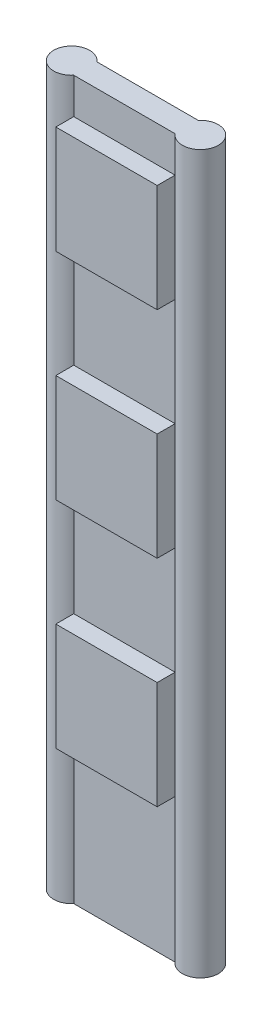
SolidWorks part; units mm, degrees
ref_plane "前基準面" through (0, 0, 0) normal (0, 0, 1) x (1, 0, 0)
ref_plane "上基準面" through (0, 0, 0) normal (0, 1, 0) x (1, 0, 0)
ref_plane "右基準面" through (0, 0, 0) normal (1, 0, 0) x (0, 0, -1)
sketch "草圖2" plane through (0, 0, 0) normal (0, 1, 0) x (1, 0, 0)
  line L0 (0, 120.0549) -> (0, -130.4945) construction
  line L1 (-141.2413, 21.3942) -> (141.2413, 21.3942)
  line L3 (-141.2413, -43.1319) -> (141.2413, -43.1319)
  line L5 (-150, 43.1319) -> (150, -43.1319) construction
  line L6 (-150, -43.1319) -> (150, 43.1319) construction
  arc A0 (-141.2413, 21.3942) -> (-141.2413, -43.1319) centre (-179.4394, -10.8688) ccw
  arc A1 (141.2413, 21.3942) -> (141.2413, -43.1319) centre (179.4394, -10.8688) cw
  point P0 (0, 0)
  point P7 (0, 0)
  dimension "D2" = 50
  dimension "D1" = 300
extrude "填料-伸長1" add sketch "草圖2" along normal blind 2000
sketch "草圖3" plane through (0, 0, 43.1319) normal (0, 0, 1) x (1, 0, 0)
  line L0 (-141.2413, 2000) -> (-141.2413, 0) construction
  line L1 (-141.2413, 400) -> (141.2413, 400)
  line L2 (-141.2413, 400) -> (-141.2413, 700)
  line L3 (-141.2413, 700) -> (141.2413, 700)
  line L4 (141.2413, 400) -> (141.2413, 700)
  line L5 (141.2413, 2000) -> (141.2413, 0) construction
  line L6 (-141.2413, 0) -> (141.2413, 0) construction
  line L7 (-141.2413, 1300) -> (141.2413, 1300)
  line L8 (-141.2413, 1000) -> (141.2413, 1000)
  line L9 (-141.2413, 1000) -> (-141.2413, 1300)
  line L10 (141.2413, 1000) -> (141.2413, 1300)
  line L11 (-141.2413, 1900) -> (141.2413, 1900)
  line L12 (-141.2413, 1600) -> (141.2413, 1600)
  line L13 (-141.2413, 1600) -> (-141.2413, 1900)
  line L14 (141.2413, 1600) -> (141.2413, 1900)
  line L19 (-141.2413, 2500) -> (141.2413, 2500) [skipped]
  line L20 (-141.2413, 2200) -> (141.2413, 2200) [skipped]
  line L21 (-141.2413, 2200) -> (-141.2413, 2500) [skipped]
  line L22 (141.2413, 2200) -> (141.2413, 2500) [skipped]
  dimension "D1" = 400
  dimension "D2" = 300
  dimension "D3" = 4
extrude "填料-伸長2" add sketch "草圖3" along normal blind 50
